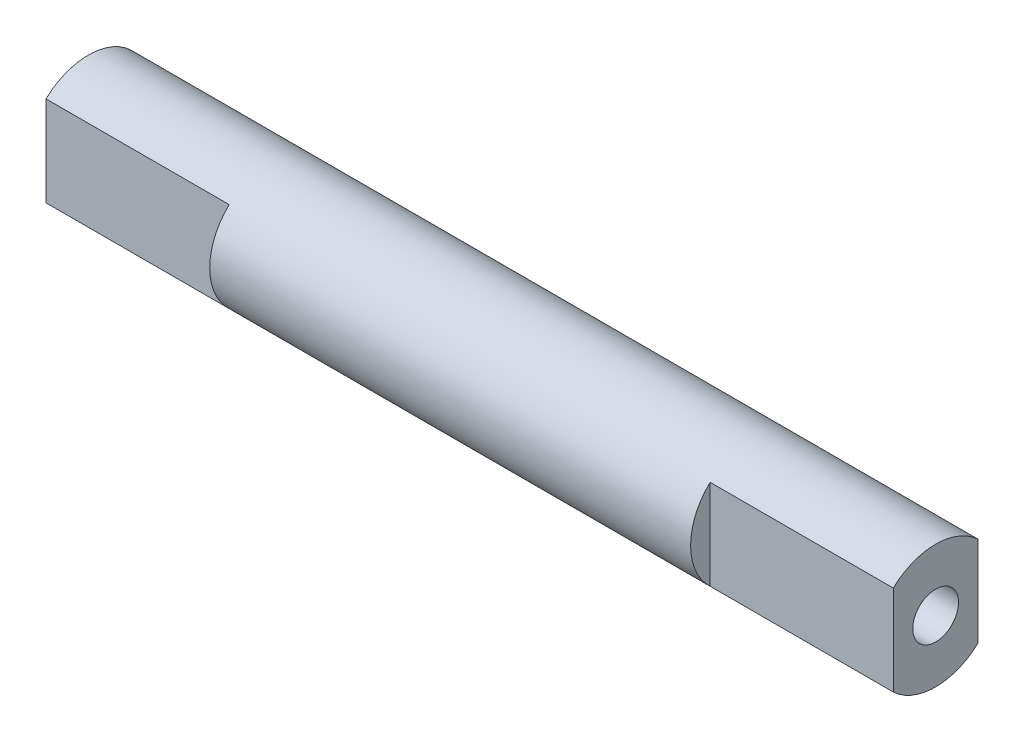
SolidWorks part; units mm, degrees
ref_plane "Front Plane" through (0, 0, 0) normal (0, 0, 1) x (1, 0, 0)
ref_plane "Top Plane" through (0, 0, 0) normal (0, 1, 0) x (1, 0, 0)
ref_plane "Right Plane" through (0, 0, 0) normal (1, 0, 0) x (0, 0, -1)
sketch "Sketch1" plane through (0, 0, 0) normal (1, 0, 0) x (0, 0, -1)
  circle A0 centre (0, 0) radius 2.7
  dimension "D1" = 5.4
extrude "Boss-Extrude1" add sketch "Sketch1" along normal mid plane 37
sketch "Sketch2" plane through (18.5, 0, 0) normal (1, 0, 0) x (0, 0, -1)
  line L0 (-1.85, 1.9666) -> (-1.85, -1.9666)
  line L1 (1.85, 1.9666) -> (1.85, -1.9666)
  arc A0 (-1.85, 1.9666) -> (-1.85, -1.9666) centre (0, 0) ccw
  arc A1 (1.85, -1.9666) -> (1.85, 1.9666) centre (0, 0) ccw
  dimension "D3" = 5.4
  dimension "D1" = 3.7
  dimension "D2" = 1.85
extrude "Cut-Extrude1" cut sketch "Sketch2" against normal blind 8
sketch "Sketch3" plane through (18.5, 0, 0) normal (1, 0, 0) x (0, 0, -1)
  circle A0 centre (0, 0) radius 1
  dimension "D1" = 2
extrude "Cut-Extrude2" cut sketch "Sketch3" against normal blind 6
mirror "Mirror1" about plane through (0, 0, 0) normal (1, 0, 0) of "Cut-Extrude1", "Cut-Extrude2"
